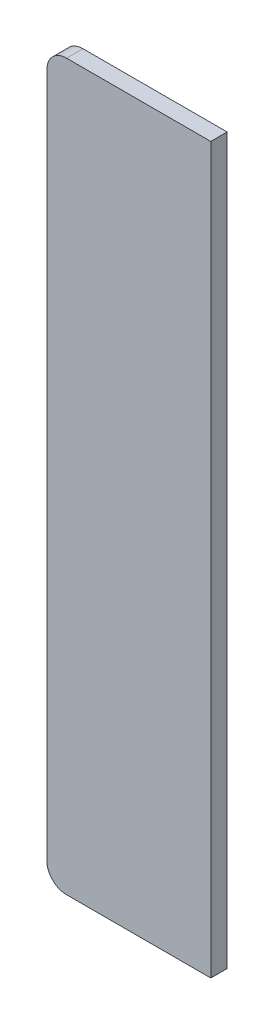
SolidWorks part; units mm, degrees
ref_plane "Front Plane" through (0, 0, 0) normal (0, 0, 1) x (1, 0, 0)
ref_plane "Top Plane" through (0, 0, 0) normal (0, 1, 0) x (1, 0, 0)
ref_plane "Right Plane" through (0, 0, 0) normal (1, 0, 0) x (0, 0, -1)
sketch "Sketch1" plane through (0, 0, 0) normal (0, 0, 1) x (1, 0, 0)
  line L1 (0, 0) -> (250, 0)
  line L2 (0, 0) -> (0, 1105)
  line L3 (0, 1105) -> (250, 1105)
  line L4 (250, 0) -> (250, 1105)
  dimension "D1" = 1105
  dimension "D2" = 250
extrude "Boss-Extrude1" add sketch "Sketch1" along normal blind 25
fillet "Fillet1" radius 30 1 edges at (0, 1105, 12.5)
fillet "Fillet2" radius 30 1 edges at (0, 0, 12.5)
